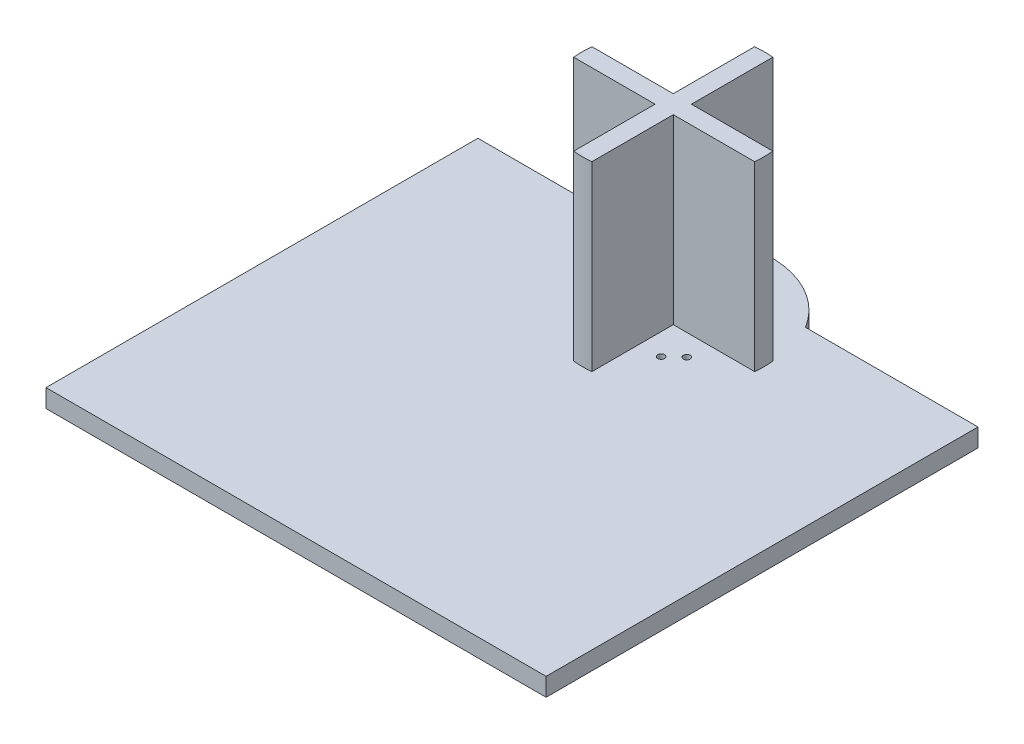
SolidWorks part; units mm, degrees
ref_plane "Front Plane" through (0, 0, 0) normal (0, 0, 1) x (1, 0, 0)
ref_plane "Top Plane" through (0, 0, 0) normal (0, 1, 0) x (1, 0, 0)
ref_plane "Right Plane" through (0, 0, 0) normal (1, 0, 0) x (0, 0, -1)
sketch "Sketch2" plane through (0, 0, 0) normal (0, 1, 0) x (1, 0, 0)
  line L1 (0, 0) -> (110, 0)
  line L2 (0, 0) -> (0, 95)
  line L3 (0, 95) -> (110, 95)
  line L4 (110, 0) -> (110, 95)
  circle A0 centre (55, 84.5433) radius 20
  dimension "D3" = 55
  dimension "D4" = 40
  dimension "D1" = 110
  dimension "D2" = 95
extrude "Boss-Extrude4" add sketch "Sketch2" along normal blind 4 contours L3 A0
sketch "Sketch3" plane through (0, 4, 0) normal (0, 1, 0) x (1, 0, 0)
  line L0 (0, 0) -> (0, 95) construction
  circle A0 centre (55, 82.9711) radius 20
  dimension "D2" = 40
  dimension "D1" = 55
extrude "Boss-Extrude5" add sketch "Sketch3" along normal blind 40 contours A0
sketch "Sketch4" plane through (0, 44, 0) normal (0, 1, 0) x (1, 0, 0)
  line L1 (53, 80.9711) -> (14.6436, 80.9711)
  line L2 (53, 80.9711) -> (53, 44.6184)
  line L3 (53, 44.6184) -> (14.6436, 44.6184)
  line L4 (14.6436, 80.9711) -> (14.6436, 44.6184)
  line L5 (53, 84.9711) -> (11.3519, 84.9711)
  line L6 (53, 84.9711) -> (53, 112.164)
  line L7 (53, 112.164) -> (11.3519, 112.164)
  line L8 (11.3519, 84.9711) -> (11.3519, 112.164)
  line L9 (57, 84.9711) -> (114.6777, 84.9711)
  line L10 (57, 84.9711) -> (57, 111.8814)
  line L11 (57, 111.8814) -> (114.6777, 111.8814)
  line L12 (114.6777, 84.9711) -> (114.6777, 111.8814)
  line L13 (57, 80.9711) -> (95.0701, 80.9711)
  line L14 (57, 80.9711) -> (57, 41.6092)
  line L15 (57, 41.6092) -> (95.0701, 41.6092)
  line L16 (95.0701, 80.9711) -> (95.0701, 41.6092)
  circle A0 centre (55, 82.9711) radius 20 construction
  circle A1 centre (55, 82.9711) radius 20 construction
  point P16 (96.7913, 42.8972)
  dimension "D1" = 2
  dimension "D2" = 2
  dimension "D3" = 2
  dimension "D4" = 2
  dimension "D5" = 2
  dimension "D6" = 2
  dimension "D7" = 2
  dimension "D8" = 2
extrude "Cut-Extrude5" cut sketch "Sketch4" against normal blind 40 contours L10 L9 L12 L11 | L14 L13 L16 L15 | L6 L5 L8 L7 | L2 L1 L4 L3
sketch "Sketch7" plane through (0, 4, 0) normal (0, 1, 0) x (1, 0, 0)
  line L0 (55, 102.9711) -> (55, 51.6276) construction
  line L1 (35, 82.9711) -> (95.5032, 82.9711) construction
  line L2 (53, 84.9711) -> (35.1003, 84.9711) construction
  arc A0 (57, 102.8708) -> (53, 102.8708) centre (55, 82.9711) ccw construction
  arc A1 (35.1003, 84.9711) -> (35.1003, 80.9711) centre (55, 82.9711) ccw construction
  circle A2 centre (45.3247, 89.6711) radius 0.75
  circle A3 centre (48.2614, 92.3869) radius 0.75
  circle A4 centre (61.7386, 92.3869) radius 0.75
  circle A5 centre (64.6753, 89.6711) radius 0.75
  circle A6 centre (64.6753, 76.2711) radius 0.75
  circle A7 centre (61.7386, 73.5552) radius 0.75
  circle A8 centre (48.2614, 73.5552) radius 0.75
  circle A9 centre (45.3247, 76.2711) radius 0.75
  point P14 (47.625, 88.3448)
  dimension "D1" = 1.5
  dimension "D2" = 4.7
  dimension "D3" = 9
  dimension "D4" = 4
extrude "Cut-Extrude6" cut sketch "Sketch7" against normal through all
